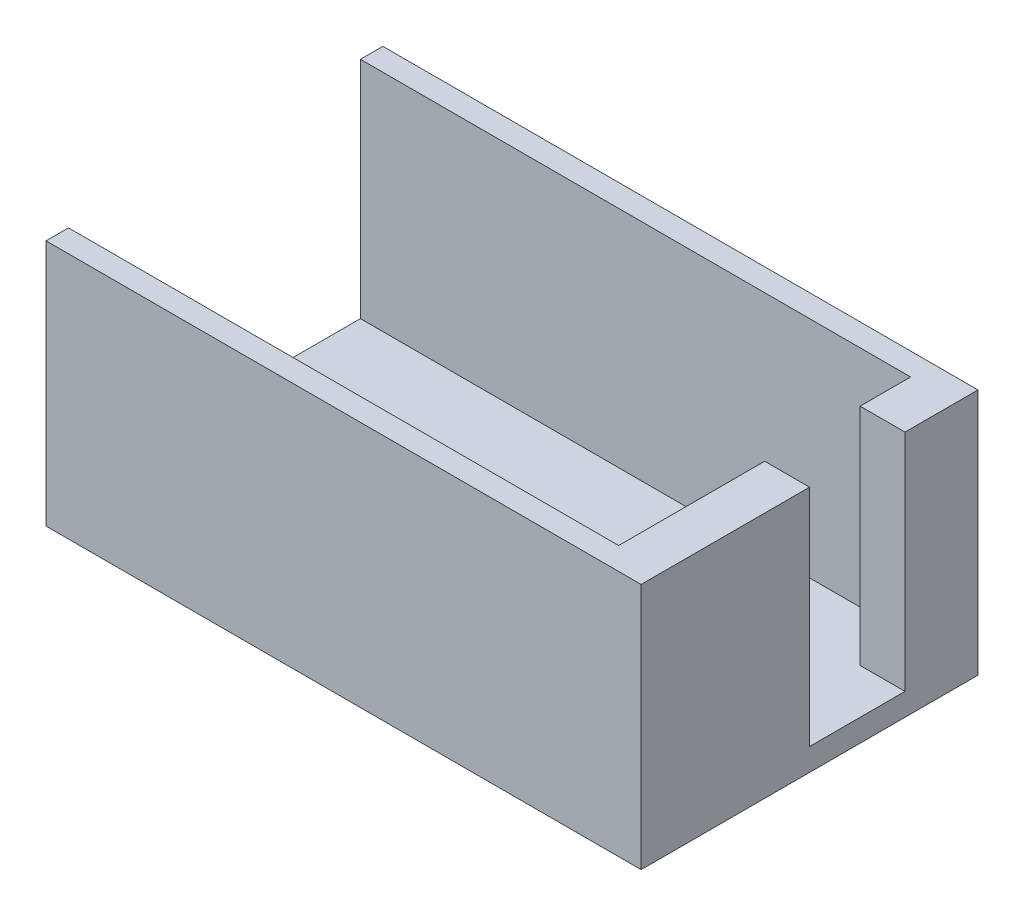
SolidWorks part; units mm, degrees
ref_plane "Front Plane" through (0, 0, 0) normal (0, 0, 1) x (1, 0, 0)
ref_plane "Top Plane" through (0, 0, 0) normal (0, 1, 0) x (1, 0, 0)
ref_plane "Right Plane" through (0, 0, 0) normal (1, 0, 0) x (0, 0, -1)
sketch "Sketch1" plane through (0, 0, 0) normal (0, 1, 0) x (1, 0, 0)
  line L1 (0, 0) -> (53, 0)
  line L2 (0, 0) -> (0, -30)
  line L3 (0, -30) -> (53, -30)
  line L4 (53, 0) -> (53, -30)
  dimension "D1" = 53
  dimension "D2" = 30
extrude "Boss-Extrude1" add sketch "Sketch1" along normal blind 2
sketch "Sketch2" plane through (0, 2, 0) normal (0, 1, 0) x (1, 0, 0)
  line L0 (0, -28) -> (49, -28)
  line L1 (49, -2) -> (0, -2)
  line L2 (49, -28) -> (49, -15)
  line L3 (49, -30) -> (49, 0) construction
  line L4 (0, 0) -> (0, -30)
  line L5 (0, -30) -> (53, -30)
  line L6 (53, -30) -> (53, 0)
  line L7 (53, 0) -> (0, 0)
  line L8 (0, 0) -> (0, -2)
  line L9 (0, -30) -> (53, -30)
  line L10 (53, -30) -> (53, -15)
  line L11 (53, 0) -> (0, 0)
  line L12 (53, -2) -> (0, -2) construction
  line L13 (0, -28) -> (53, -28) construction
  line L14 (0, -28) -> (0, -30)
  line L15 (49, -6.5) -> (53, -6.5)
  line L16 (49, -15) -> (53, -15)
  line L17 (49, -6.5) -> (49, -2)
  line L18 (53, -6.5) -> (53, 0)
  line L19 (53, -30) -> (53, 0) construction
  dimension "D5" = 6.5
  dimension "D6" = 15
  dimension "D1" = 0
  dimension "D2" = 2
  dimension "D3" = 2
  dimension "D4" = 4
extrude "Boss-Extrude2" add sketch "Sketch2" along normal blind 20
